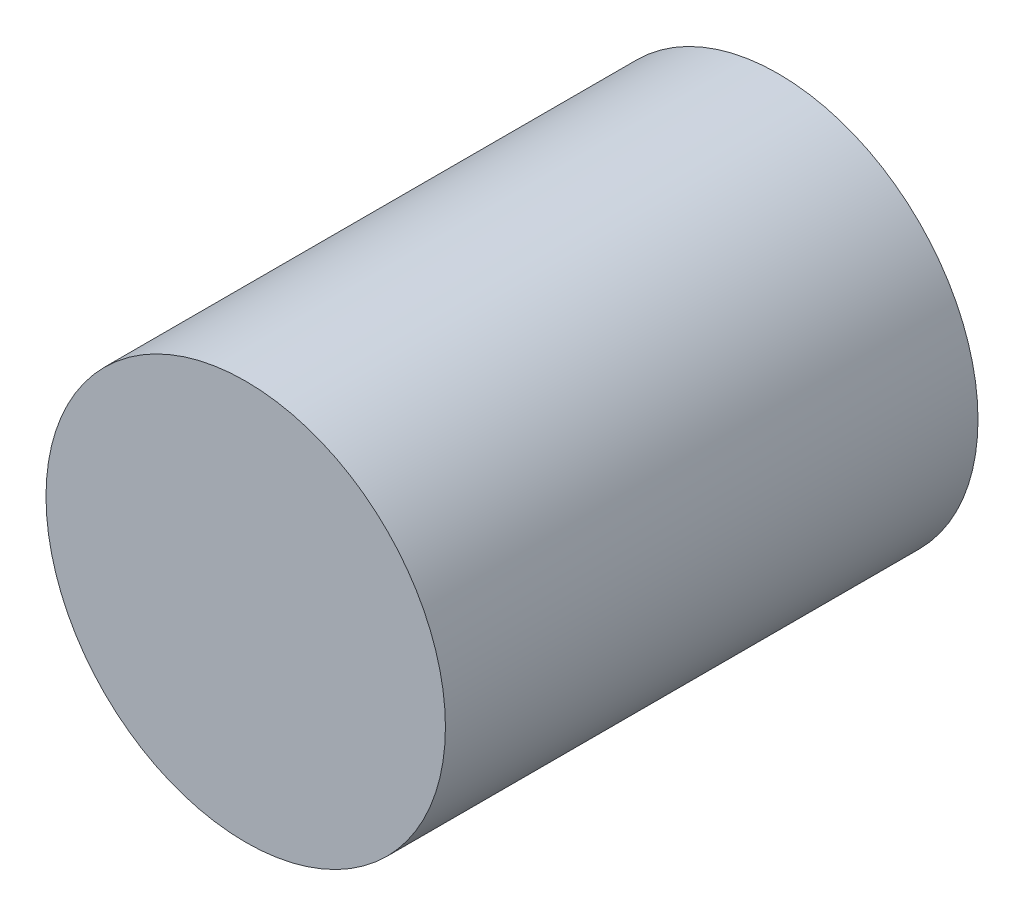
SolidWorks part; units mm, degrees
ref_plane "Front Plane" through (0, 0, 0) normal (0, 0, 1) x (1, 0, 0)
ref_plane "Top Plane" through (0, 0, 0) normal (0, 1, 0) x (1, 0, 0)
ref_plane "Right Plane" through (0, 0, 0) normal (1, 0, 0) x (0, 0, -1)
sketch "Sketch1" plane through (0, 0, 0) normal (0, 0, 1) x (1, 0, 0)
  circle A0 centre (0, 0) radius 1.5
  dimension "D1" = 3
extrude "Boss-Extrude1" add sketch "Sketch1" along normal blind 4
